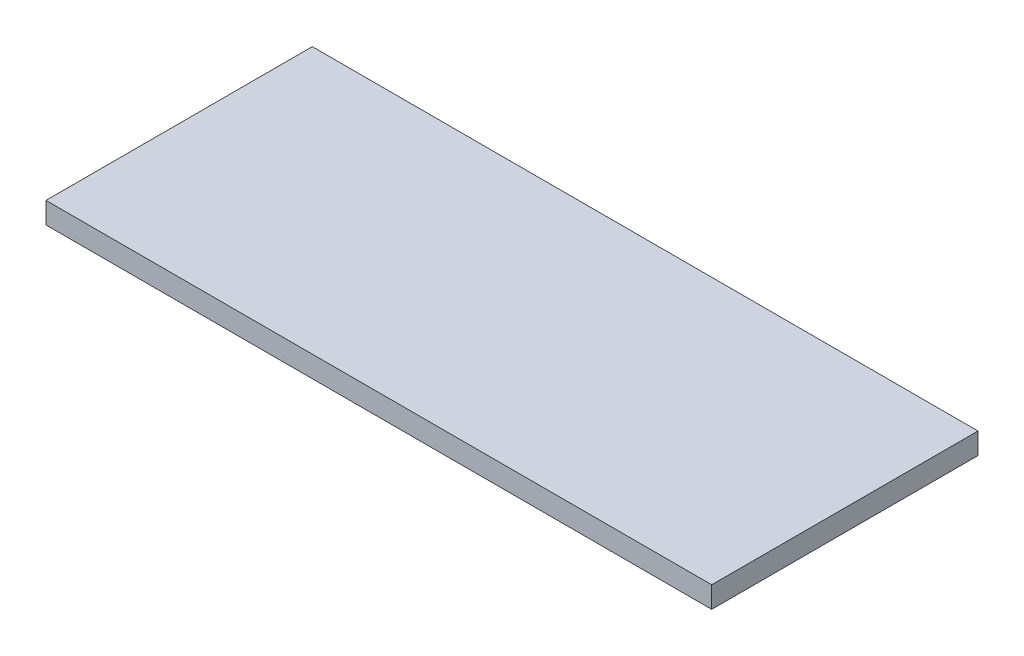
SolidWorks part; units mm, degrees
ref_plane "Front Plane" through (0, 0, 0) normal (0, 0, 1) x (1, 0, 0)
ref_plane "Top Plane" through (0, 0, 0) normal (0, 1, 0) x (1, 0, 0)
ref_plane "Right Plane" through (0, 0, 0) normal (1, 0, 0) x (0, 0, -1)
sketch "Sketch1" plane through (0, 0, 0) normal (0, 1, 0) x (1, 0, 0)
  line L1 (0, 0) -> (50, 0)
  line L2 (0, 0) -> (0, 20)
  line L3 (0, 20) -> (50, 20)
  line L4 (50, 0) -> (50, 20)
  dimension "D1" = 20
  dimension "D2" = 50
extrude "Boss-Extrude1" add sketch "Sketch1" along normal blind 1.6
sketch "Sketch2" plane through (0, 1.6, 0) normal (0, 1, 0) x (1, 0, 0)
  line L0 (50, 20) -> (0, 20) construction
  line L2 (7.5, 20) -> (7.5, 0)
  line L4 (10.5, 20) -> (10.5, 0)
  line L5 (0, 0) -> (50, 0) construction
  line L6 (0, 20) -> (0, 0) construction
  line L7 (9, 0) -> (9, 19.5)
  line L8 (9, 19.5) -> (7.5, 19.5)
  line L9 (10.5, 10) -> (9, 10)
  line L10 (12.5, 20) -> (12.5, 0)
  line L11 (14, 0) -> (14, 19.5)
  line L12 (15.5, 20) -> (15.5, 0)
  line L13 (15.5, 10) -> (14, 10)
  line L14 (14, 19.5) -> (12.5, 19.5)
  line L15 (17.5, 20) -> (17.5, 0)
  line L16 (19, 0) -> (19, 19.5)
  line L17 (20.5, 20) -> (20.5, 0)
  line L18 (20.5, 10) -> (19, 10)
  line L19 (19, 19.5) -> (17.5, 19.5)
  line L20 (22.5, 20) -> (22.5, 0)
  line L21 (24, 0) -> (24, 19.5)
  line L22 (25.5, 20) -> (25.5, 0)
  line L23 (25.5, 10) -> (24, 10)
  line L24 (24, 19.5) -> (22.5, 19.5)
  line L25 (27.5, 20) -> (27.5, 0)
  line L26 (29, 0) -> (29, 19.5)
  line L27 (30.5, 20) -> (30.5, 0)
  line L28 (30.5, 10) -> (29, 10)
  line L29 (29, 19.5) -> (27.5, 19.5)
  line L30 (32.5, 20) -> (32.5, 0)
  line L31 (34, 0) -> (34, 19.5)
  line L32 (35.5, 20) -> (35.5, 0)
  line L33 (35.5, 10) -> (34, 10)
  line L34 (34, 19.5) -> (32.5, 19.5)
  line L35 (37.5, 20) -> (37.5, 0)
  line L36 (39, 0) -> (39, 19.5)
  line L37 (40.5, 20) -> (40.5, 0)
  line L38 (40.5, 10) -> (39, 10)
  line L39 (39, 19.5) -> (37.5, 19.5)
  dimension "D1" = 7.5
  dimension "D2" = 3
  dimension "D3" = 1.5
  dimension "D5" = 0.5
  dimension "D6" = 10
  dimension "D4" = 7
sketch "Sketch3" plane through (0, 1.6, 0) normal (0, 1, 0) x (1, 0, 0)
  line L0 (7.5, 0) -> (10.5, 0) construction
  line L1 (10.5, 10) -> (9, 10) construction
  line L2 (9, 19.5) -> (7.5, 19.5) construction
  line L3 (9.75, 5.5) -> (9.75, 14.5) construction
  line L4 (8.25, 19.5) -> (8.25, 0.75) construction
  circle A0 centre (8.25, 0.75) radius 0.375
  circle A1 centre (9.75, 0.75) radius 0.375
  circle A2 centre (9.75, 5.5) radius 0.375
  circle A3 centre (9.75, 14.5) radius 0.375
  circle A4 centre (13.25, 0.75) radius 0.375
  circle A5 centre (14.75, 0.75) radius 0.375
  circle A6 centre (14.75, 14.5) radius 0.375
  circle A7 centre (14.75, 5.5) radius 0.375
  circle A8 centre (18.25, 0.75) radius 0.375
  circle A9 centre (19.75, 0.75) radius 0.375
  circle A10 centre (19.75, 14.5) radius 0.375
  circle A11 centre (19.75, 5.5) radius 0.375
  circle A12 centre (23.25, 0.75) radius 0.375
  circle A13 centre (24.75, 0.75) radius 0.375
  circle A14 centre (24.75, 14.5) radius 0.375
  circle A15 centre (24.75, 5.5) radius 0.375
  circle A16 centre (28.25, 0.75) radius 0.375
  circle A17 centre (29.75, 0.75) radius 0.375
  circle A18 centre (29.75, 14.5) radius 0.375
  circle A19 centre (29.75, 5.5) radius 0.375
  circle A20 centre (33.25, 0.75) radius 0.375
  circle A21 centre (34.75, 0.75) radius 0.375
  circle A22 centre (34.75, 14.5) radius 0.375
  circle A23 centre (34.75, 5.5) radius 0.375
  circle A24 centre (38.25, 0.75) radius 0.375
  circle A25 centre (39.75, 0.75) radius 0.375
  circle A26 centre (39.75, 14.5) radius 0.375
  circle A27 centre (39.75, 5.5) radius 0.375
  point P8 (8.25, 19.5)
  point P12 (9.75, 10)
  point P16 (9.75, 10)
  dimension "D1" = 0.75
  dimension "D3" = 9
  dimension "D2" = 0.75
  dimension "D4" = 7
